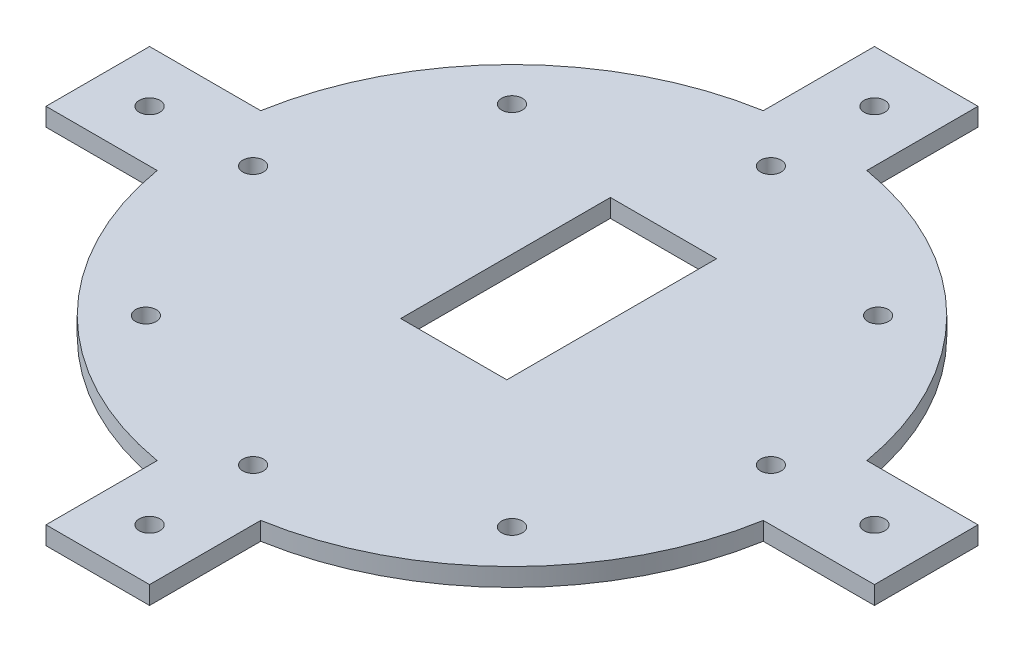
SolidWorks part; units mm, degrees
material "Balsa"
ref_plane "Alzado" through (0, 0, 0) normal (0, 0, 1) x (1, 0, 0)
ref_plane "Planta" through (0, 0, 0) normal (0, 1, 0) x (1, 0, 0)
ref_plane "Vista lateral" through (0, 0, 0) normal (1, 0, 0) x (0, 0, -1)
sketch "Croquis1" plane through (0, 0, 0) normal (0, 1, 0) x (1, 0, 0)
  line L0 (-10, -58.5304) -> (-10, -80)
  line L1 (-10, 80) -> (10, 80)
  line L2 (-10, 80) -> (-10, 58.5304)
  line L3 (-10, -80) -> (10, -80)
  line L4 (10, 80) -> (10, 58.5304)
  line L5 (58.5304, 10) -> (80, 10)
  line L6 (-80, -10) -> (-58.5304, -10)
  line L7 (-80, -10) -> (-80, 10)
  line L8 (-80, 10) -> (-58.5304, 10)
  line L9 (10, -58.5304) -> (10, -80)
  line L10 (80, -10) -> (80, 10)
  line L15 (58.5304, -10) -> (80, -10)
  arc A0 (-10, 58.5304) -> (-58.5304, 10) centre (0, 0) ccw
  circle A1 centre (0, 42) radius 1.8585
  arc A2 (10, -58.5304) -> (58.5304, -10) centre (0, 0) ccw
  arc A3 (-58.5304, -10) -> (-10, -58.5304) centre (0, 0) ccw
  arc A4 (58.5304, 10) -> (10, 58.5304) centre (0, 0) ccw
  dimension "D1" = 42
  dimension "D6" = 80
  dimension "D2" = 160
  dimension "D3" = 20
  dimension "D4" = 20
  dimension "D5" = 160
  dimension "D7" = 80
  dimension "D8" = 10
  dimension "D9" = 10
extrude "Saliente-Extruir1" add sketch "Croquis1" along normal blind 3.5 contours A0 L8 L7 L6 A3 L0 L3 L9 A2 L15 L10 L5 A4 L4 L1 L2
sketch "Croquis2" plane through (0, 3.5, 0) normal (0, 1, 0) x (1, 0, 0)
  circle A0 centre (0, 50) radius 2
  dimension "D1" = 50
extrude "Cortar-Extruir1" cut sketch "Croquis2" against normal up to next (3.5 mm away)
pattern_circular "MatrizC1" count 8 every 45 about axis through (0, 0, 0) along (0, 1, 0) of "Cortar-Extruir1"
sketch "Croquis3" plane through (0, 3.5, 0) normal (0, 1, 0) x (1, 0, 0)
  line L5 (10.25, 29.25) -> (-10.25, 29.25)
  line L6 (10.25, 29.25) -> (10.25, -11.25)
  line L7 (10.25, -11.25) -> (-10.25, -11.25)
  line L8 (-10.25, 29.25) -> (-10.25, -11.25)
  line L9 (10.25, 29.25) -> (-10.25, -11.25) construction
  line L10 (10.25, -11.25) -> (-10.25, 29.25) construction
  point P0 (0, 9)
  point P1 (0, 9)
  dimension "D1" = 9
  dimension "D2" = 40.5
  dimension "D3" = 20.5
extrude "Cortar-Extruir2" cut sketch "Croquis3" against normal up to next
sketch "Croquis4" plane through (0, 3.5, 0) normal (0, 1, 0) x (1, 0, 0)
  circle A0 centre (0, 70) radius 2
  circle A1 centre (70, 0) radius 2
  circle A2 centre (0, -70) radius 2
  circle A3 centre (-70, 0) radius 2
  point P12 (0, 0)
  dimension "D1" = 70
  dimension "D2" = 4
extrude "Cortar-Extruir3" cut sketch "Croquis4" against normal up to next
